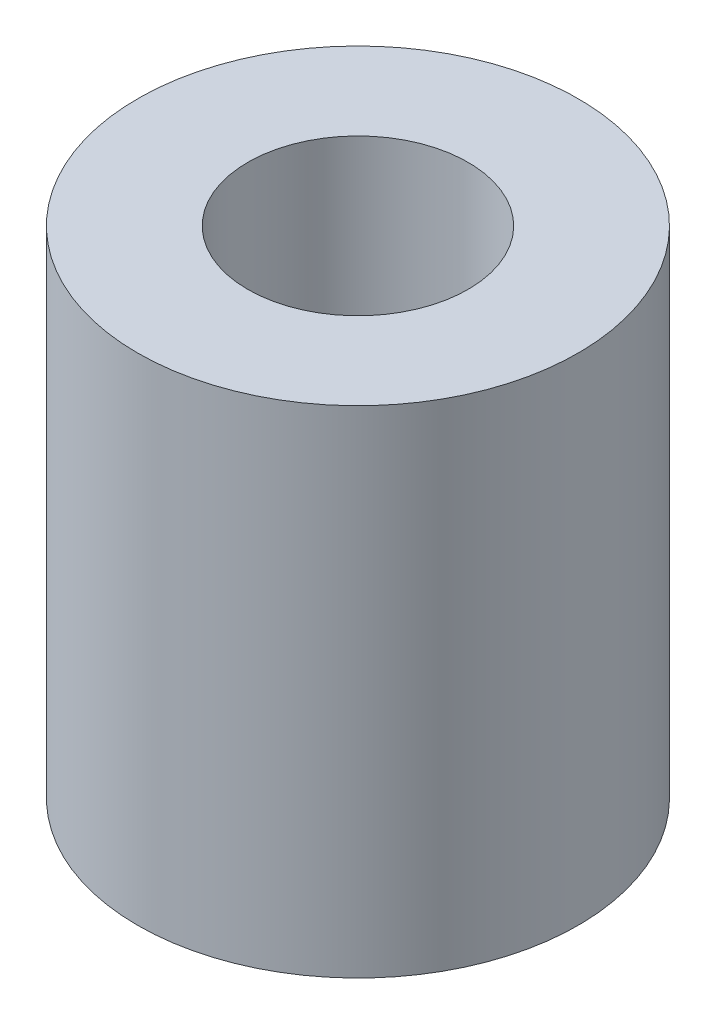
SolidWorks part; units mm, degrees
ref_plane "정면" through (0, 0, 0) normal (0, 0, 1) x (1, 0, 0)
ref_plane "윗면" through (0, 0, 0) normal (0, 1, 0) x (1, 0, 0)
ref_plane "우측면" through (0, 0, 0) normal (1, 0, 0) x (0, 0, -1)
sketch "스케치1" plane through (0, 0, 0) normal (0, 1, 0) x (1, 0, 0)
  circle A0 centre (0, 0) radius 6
  circle A1 centre (0, 0) radius 3
  dimension "D1" = 12
  dimension "D2" = 6
extrude "보스-돌출1" add sketch "스케치1" along normal blind 13.5 contours A0 | A1
